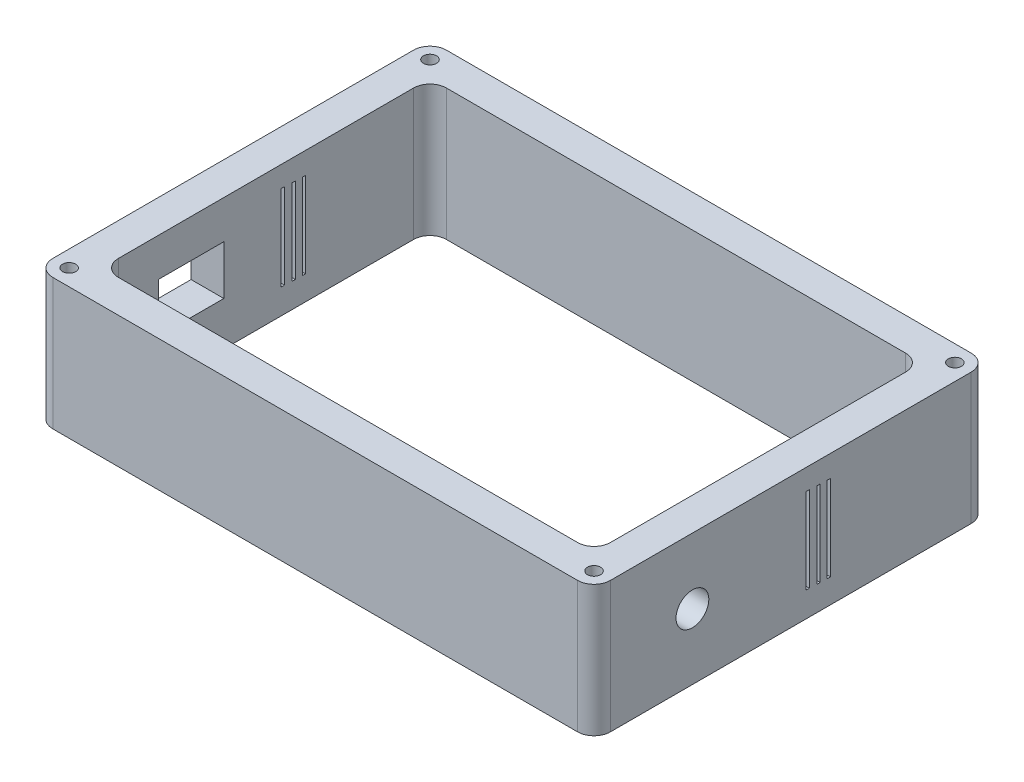
SolidWorks part; units mm, degrees
ref_plane "Front Plane" through (0, 0, 0) normal (0, 0, 1) x (1, 0, 0)
ref_plane "Top Plane" through (0, 0, 0) normal (0, 1, 0) x (1, 0, 0)
ref_plane "Right Plane" through (0, 0, 0) normal (1, 0, 0) x (0, 0, -1)
sketch "Sketch1" plane through (0, 0, 0) normal (0, 1, 0) x (1, 0, 0)
  line L1 (75, -50) -> (-75, -50)
  line L2 (75, -50) -> (75, 50)
  line L3 (75, 50) -> (-75, 50)
  line L4 (-75, -50) -> (-75, 50)
  line L5 (75, -50) -> (-75, 50) construction
  line L6 (75, 50) -> (-75, -50) construction
  point P0 (0, 0)
  dimension "D1" = 150
  dimension "D2" = 100
extrude "Extrude-Thin1" add sketch "Sketch1" along normal blind 40 thin contours L3 L4 L1 L2 thin type one direction wall 10
sketch "Sketch2" plane through (85, 0, 0) normal (1, 0, 0) x (0, 0, -1)
  line L2 (-60, 40) -> (-60, 0) construction
  line L3 (-60, 0) -> (60, 0) construction
  circle A0 centre (-30, 20) radius 5
  dimension "D1" = 30
  dimension "D2" = 20
extrude "Cut-Extrude1" cut sketch "Sketch2" against normal blind 10 contours A0
sketch "Sketch3" plane through (0, 40, 0) normal (0, 1, 0) x (1, 0, 0)
  line L0 (-85, -60) -> (-85, 60) construction
  line L1 (85, 60) -> (-85, 60) construction
  line L2 (85, -60) -> (-85, -60) construction
  line L3 (85, -60) -> (85, 60) construction
  circle A0 centre (-80, 55) radius 2
  circle A1 centre (-80, -55) radius 2
  circle A2 centre (80, -55) radius 2
  circle A3 centre (80, 55) radius 2
  dimension "D1" = 5
  dimension "D5" = 5
  dimension "D6" = 5
  dimension "D2" = 170
  dimension "D3" = 170
  dimension "D4" = 5
hole_wizard "Ø4.0mm Dowel Hole1" positions "Sketch7" profile "Sketch8" hole size "Ø4.0" standard "ANSI Metric"
sketch "Sketch7" plane through (0, 40, 0) normal (0, 1, 0) x (1, 0, 0)
  point P0 (-80, 55)
sketch "Sketch8" plane through (-80, 40, -55) normal (1, 0, 0) x (0, 0, 1)
  line L0 (0, 0) -> (0, 6.2017)
  line L1 (0, 6.2017) -> (2, 5)
  line L2 (2, 5) -> (2, 0)
  line L5 (2, 0) -> (0, 0)
  line L10 (0, 6.2017) -> (-2, 5) construction
  line L11 (0, -6.35) -> (0, 107.95) construction
  dimension "Hole Dia." = 4
  dimension "Hole Depth" = 5
  dimension "Drill Angle" = 118
hole_wizard "Ø4.0mm Dowel Hole2" positions "Sketch9" profile "Sketch10" hole size "Ø4.0" standard "ANSI Metric"
sketch "Sketch9" plane through (0, 40, 0) normal (0, 1, 0) x (1, 0, 0)
  point P0 (-80, -55)
sketch "Sketch10" plane through (-80, 40, 55) normal (1, 0, 0) x (0, 0, 1)
  line L0 (0, 0) -> (0, 6.2017)
  line L1 (0, 6.2017) -> (2, 5)
  line L2 (2, 5) -> (2, 0)
  line L5 (2, 0) -> (0, 0)
  line L10 (0, 6.2017) -> (-2, 5) construction
  line L11 (0, -6.35) -> (0, 107.95) construction
  dimension "Hole Dia." = 4
  dimension "Hole Depth" = 5
  dimension "Drill Angle" = 118
hole_wizard "Ø4.0mm Dowel Hole3" positions "Sketch11" profile "Sketch12" hole size "Ø4.0" standard "ANSI Metric"
sketch "Sketch11" plane through (0, 40, 0) normal (0, 1, 0) x (1, 0, 0)
  point P0 (80, -55)
sketch "Sketch12" plane through (80, 40, 55) normal (1, 0, 0) x (0, 0, 1)
  line L0 (0, 0) -> (0, 6.2017)
  line L1 (0, 6.2017) -> (2, 5)
  line L2 (2, 5) -> (2, 0)
  line L5 (2, 0) -> (0, 0)
  line L10 (0, 6.2017) -> (-2, 5) construction
  line L11 (0, -6.35) -> (0, 107.95) construction
  dimension "Hole Dia." = 4
  dimension "Hole Depth" = 5
  dimension "Drill Angle" = 118
hole_wizard "Ø4.0mm Dowel Hole4" positions "Sketch13" profile "Sketch14" hole size "Ø4.0" standard "ANSI Metric"
sketch "Sketch13" plane through (0, 40, 0) normal (0, 1, 0) x (1, 0, 0)
  point P0 (80, 55)
sketch "Sketch14" plane through (80, 40, -55) normal (1, 0, 0) x (0, 0, 1)
  line L0 (0, 0) -> (0, 6.2017)
  line L1 (0, 6.2017) -> (2, 5)
  line L2 (2, 5) -> (2, 0)
  line L5 (2, 0) -> (0, 0)
  line L10 (0, 6.2017) -> (-2, 5) construction
  line L11 (0, -6.35) -> (0, 107.95) construction
  dimension "Hole Dia." = 4
  dimension "Hole Depth" = 5
  dimension "Drill Angle" = 118
sketch "Sketch15" plane through (-85, 0, 0) normal (-1, 0, 0) x (0, 0, 1)
  line L1 (12.8376, 28.3406) -> (32.8376, 28.3406)
  line L2 (12.8376, 28.3406) -> (12.8376, 13.3406)
  line L3 (12.8376, 13.3406) -> (32.8376, 13.3406)
  line L4 (32.8376, 28.3406) -> (32.8376, 13.3406)
  line L5 (12.8376, 28.3406) -> (32.8376, 13.3406) construction
  line L6 (12.8376, 13.3406) -> (32.8376, 28.3406) construction
  point P0 (22.8376, 20.8406)
  point P5 (12.6097, 24.6236)
  point P7 (22.8376, 20.8406)
  dimension "D1" = 20
  dimension "D2" = 15
extrude "Cut-Extrude7" cut sketch "Sketch15" against normal blind 10
fillet "Fillet1" radius 5 4 edges at (85, 20, -60) (-85, 20, -60) (-85, 20, 60) (85, 20, 60)
sketch "Sketch16" plane through (85, 0, 0) normal (1, 0, 0) x (0, 0, -1)
  line L5 (4.6236, 33.6342) -> (5.6236, 33.6342)
  line L6 (4.6236, 33.6342) -> (4.6236, 7.6342)
  line L7 (4.6236, 7.6342) -> (5.6236, 7.6342)
  line L8 (5.6236, 33.6342) -> (5.6236, 7.6342)
  dimension "D1" = 1
  dimension "D2" = 26
extrude "Cut-Extrude8" cut sketch "Sketch16" against normal through all both and the other way through all contours L6 L7 L8 L5
sketch "Sketch17" plane through (85, 0, 0) normal (1, 0, 0) x (0, 0, -1)
  line L1 (7.9669, 33.4768) -> (8.9669, 33.4768)
  line L2 (7.9669, 33.4768) -> (7.9669, 7.4768)
  line L3 (7.9669, 7.4768) -> (8.9669, 7.4768)
  line L4 (8.9669, 33.4768) -> (8.9669, 7.4768)
  point P4 (8.6867, 33.3968)
  point P5 (8.1263, 7.4768)
  dimension "D1" = 1
  dimension "D2" = 26
extrude "Cut-Extrude9" cut sketch "Sketch17" against normal through all both and the other way through all contours L4 L3 L2 L1
sketch "Sketch19" plane through (85, 0, 0) normal (1, 0, 0) x (0, 0, -1)
  line L1 (11.0686, 33.3903) -> (12.0686, 33.3903)
  line L2 (11.0686, 33.3903) -> (11.0686, 7.3903)
  line L3 (11.0686, 7.3903) -> (12.0686, 7.3903)
  line L4 (12.0686, 33.3903) -> (12.0686, 7.3903)
  dimension "D1" = 1
  dimension "D2" = 26
extrude "Cut-Extrude10" cut sketch "Sketch19" against normal through all both and the other way through all contours L4 L3 L2 L1
fillet "Fillet2" radius 5 4 edges at (75, 20, -50) (-75, 20, -50) (-75, 20, 50) (75, 20, 50)
